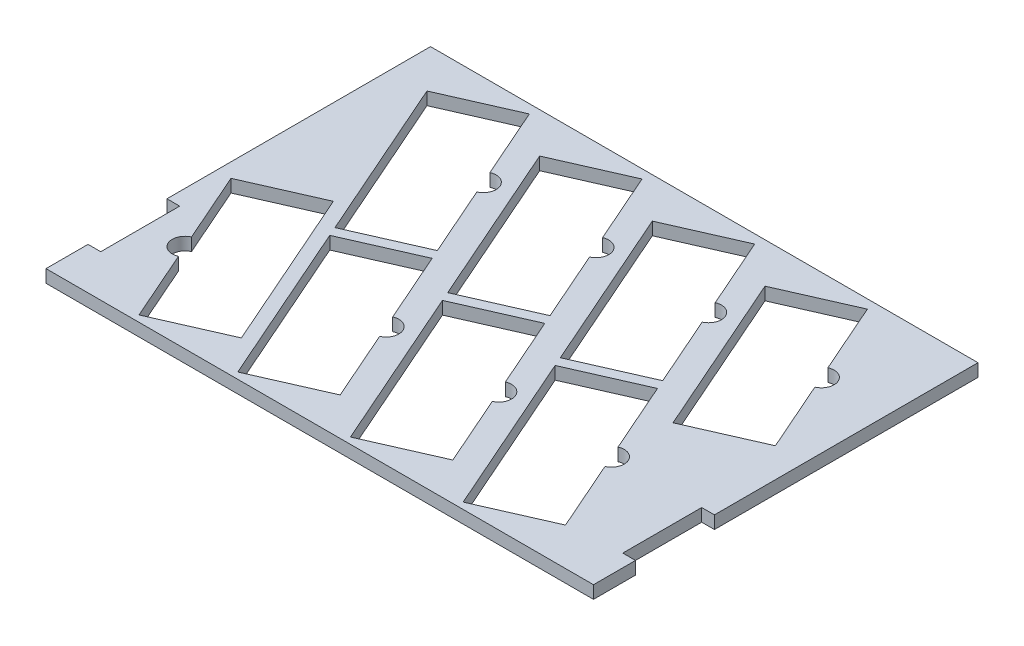
SolidWorks part; units mm, degrees
ref_plane "Front Plane" through (0, 0, 0) normal (0, 0, 1) x (1, 0, 0)
ref_plane "Top Plane" through (0, 0, 0) normal (0, 1, 0) x (1, 0, 0)
ref_plane "Right Plane" through (0, 0, 0) normal (1, 0, 0) x (0, 0, -1)
sketch "Sketch1" plane through (0, 0, 0) normal (0, 1, 0) x (1, 0, 0)
  line L0 (-215, -151) -> (-215, 151)
  line L1 (-215, 151) -> (215, 151)
  line L3 (-215, -151) -> (215, -151)
  line L15 (-97.7123, 119.4252) -> (-41.8815, 144)
  line L44 (-186.2118, 119.4252) -> (-130.381, 144)
  line L61 (-186.2118, 119.4252) -> (-129.4078, -9.6263)
  line L62 (-130.381, 144) -> (-106.0076, 88.6268)
  line L63 (-129.4078, -9.6263) -> (-73.577, 14.9484)
  line L76 (-97.9503, 70.3216) -> (-73.577, 14.9484)
  line L77 (-41.8815, 144) -> (-17.5081, 88.6268)
  line L78 (-9.4508, 70.3216) -> (14.9225, 14.9484)
  line L79 (-40.9083, -9.6263) -> (14.9225, 14.9484)
  line L80 (-97.7123, 119.4252) -> (-40.9083, -9.6263)
  line L81 (-9.2128, 119.4252) -> (46.618, 144)
  line L82 (46.618, 144) -> (70.9914, 88.6268)
  line L83 (79.0486, 70.3216) -> (103.422, 14.9484)
  line L84 (47.5912, -9.6263) -> (103.422, 14.9484)
  line L85 (-9.2128, 119.4252) -> (47.5912, -9.6263)
  line L86 (79.2867, 119.4252) -> (135.1175, 144)
  line L87 (135.1175, 144) -> (159.4908, 88.6268)
  line L88 (167.5481, 70.3216) -> (191.9215, 14.9484)
  line L89 (136.0906, -9.6263) -> (191.9215, 14.9484)
  line L90 (79.2867, 119.4252) -> (136.0906, -9.6263)
  line L91 (-126.1849, -16.9484) -> (-70.3541, 7.6263)
  line L92 (215, -151) -> (215, 151)
  line L93 (-203.7586, -16.9484) -> (-147.9277, 7.6263)
  line L94 (-203.7586, -16.9484) -> (-179.3852, -72.3216)
  line L96 (-146.9546, -146) -> (-91.1238, -121.4252)
  line L97 (0, 0) -> (0, 181.9408) construction
  line L98 (-215, -101) -> (-205, -101)
  line L116 (-126.1849, -16.9484) -> (-69.381, -146)
  line L117 (-70.3541, 7.6263) -> (-45.9808, -47.7469)
  line L118 (-69.381, -146) -> (-13.5501, -121.4252)
  line L119 (-147.9277, 7.6263) -> (-91.1238, -121.4252)
  line L120 (-171.3279, -90.6268) -> (-146.9546, -146)
  line L121 (-37.9235, -66.052) -> (-13.5501, -121.4252)
  line L122 (-215, -101) -> (-215, -118)
  line L123 (-215, -118) -> (-205, -118)
  line L124 (-37.6854, -16.9484) -> (18.1454, 7.6263)
  line L125 (18.1454, 7.6263) -> (42.5187, -47.7469)
  line L126 (-205, -101) -> (-205, -118)
  line L127 (50.576, -66.052) -> (74.9494, -121.4252)
  line L128 (19.1185, -146) -> (74.9494, -121.4252)
  line L129 (-37.6854, -16.9484) -> (19.1185, -146)
  line L130 (50.8141, -16.9484) -> (106.6449, 7.6263)
  line L131 (106.6449, 7.6263) -> (131.0182, -47.7469)
  line L132 (139.0755, -66.052) -> (163.4488, -121.4252)
  line L133 (107.618, -146) -> (163.4488, -121.4252)
  line L134 (50.8141, -16.9484) -> (107.618, -146)
  line L135 (215, -118) -> (205, -118)
  line L136 (205, -101) -> (205, -118)
  line L137 (215, -101) -> (205, -101)
  line L138 (215, -101) -> (215, -118)
  line L140 (205, -101) -> (215, -101)
  line L141 (205, -101) -> (205, -56)
  line L142 (205, -56) -> (215, -56)
  line L143 (215, -101) -> (215, -56)
  line L144 (-215, -101) -> (-205, -101)
  line L145 (-215, -101) -> (-215, -56)
  line L146 (-215, -56) -> (-205, -56)
  line L147 (-205, -101) -> (-205, -56)
  arc A4 (-106.0076, 88.6268) -> (-97.9503, 70.3216) centre (-101.979, 79.4742) cw
  arc A5 (-17.5081, 88.6268) -> (-9.4508, 70.3216) centre (-13.4795, 79.4742) cw
  arc A6 (70.9914, 88.6268) -> (79.0486, 70.3216) centre (75.02, 79.4742) cw
  arc A7 (159.4908, 88.6268) -> (167.5481, 70.3216) centre (163.5195, 79.4742) cw
  arc A9 (-179.3852, -72.3216) -> (-171.3279, -90.6268) centre (-175.3566, -81.4742) ccw
  arc A10 (-45.9808, -47.7469) -> (-37.9235, -66.052) centre (-41.9521, -56.8994) cw
  arc A11 (42.5187, -47.7469) -> (50.576, -66.052) centre (46.5474, -56.8994) cw
  arc A12 (131.0182, -47.7469) -> (139.0755, -66.052) centre (135.0469, -56.8994) cw
  point P0 (0, 0)
  point P13 (-32.7995, -52.8708)
  point P51 (-92.8264, 83.5029)
  dimension "D3" = 151
  dimension "D12" = 10
  dimension "D14" = 10
  dimension "D15" = 8
  dimension "D18" = 5
  dimension "D24" = 10
  dimension "D13" = 141
  dimension "D10" = 10
  dimension "D20" = 17
  dimension "D1" = 430
  dimension "D2" = 302
  dimension "D4" = 7
  dimension "D5" = 4
  dimension "D6" = 141
  dimension "D7" = 215
  dimension "D8" = 70.5
  dimension "D11" = 5
  dimension "D16" = 61
  dimension "D17" = 141
  dimension "D19" = 10
  dimension "D21" = 3
  dimension "D22" = 20
  dimension "D23" = 60.5
  dimension "D25" = 60.5
  dimension "D26" = 10
  dimension "D27" = 33
  dimension "D28" = 10
  dimension "D29" = 45
  dimension "D30" = 45
  dimension "D9" = 51.5512
extrude "Boss-Extrude1" add sketch "Sketch1" against normal blind 10 contours L3 L92 L1 L0 A9 L94 L93 L119 L96 L120 L62 A4 L76 L63 L61 L44 L77 A5 L78 L79 L80 L15 L82 A6 L83 L84 L85 L81 L87 A7 L88 L89 L90 L86 L117 A10 L121 L118 L116 L91 L125 A11 L127 L128
